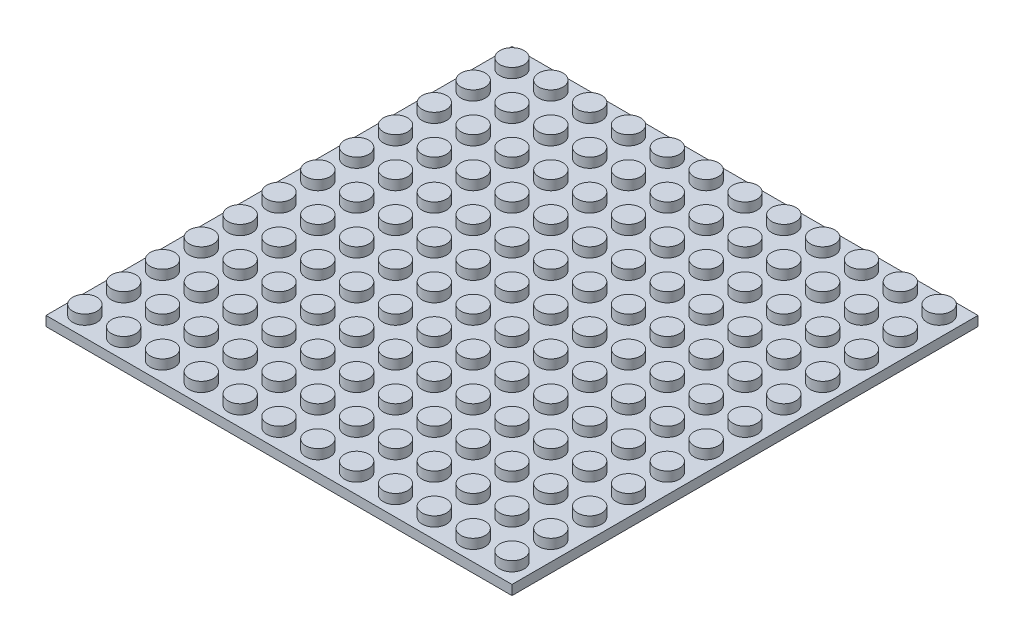
SolidWorks part; units mm, degrees
ref_plane "Front Plane" through (0, 0, 0) normal (0, 0, 1) x (1, 0, 0)
ref_plane "Top Plane" through (0, 0, 0) normal (0, 1, 0) x (1, 0, 0)
ref_plane "Right Plane" through (0, 0, 0) normal (1, 0, 0) x (0, 0, -1)
sketch "Sketch1" plane through (0, 0, 0) normal (0, 1, 0) x (1, 0, 0)
  line L1 (0, 0) -> (96, 0)
  line L2 (0, 0) -> (0, 96)
  line L3 (0, 96) -> (96, 96)
  line L4 (96, 0) -> (96, 96)
  dimension "D1" = 96
  dimension "D2" = 96
extrude "Boss-Extrude1" add sketch "Sketch1" along normal blind 2
sketch "Sketch2" plane through (0, 2, 0) normal (0, 1, 0) x (1, 0, 0)
  line L0 (0, 0) -> (96, 0) construction
  line L1 (0, 96) -> (0, 0) construction
  line L2 (4, 4) -> (12, 4) construction
  circle A0 centre (4, 4) radius 2.5
  circle A1 centre (12, 4) radius 2.5
  circle A2 centre (20, 4) radius 2.5
  circle A3 centre (28, 4) radius 2.5
  circle A4 centre (36, 4) radius 2.5
  circle A5 centre (44, 4) radius 2.5
  circle A6 centre (52, 4) radius 2.5
  circle A7 centre (60, 4) radius 2.5
  circle A8 centre (68, 4) radius 2.5
  circle A9 centre (76, 4) radius 2.5
  circle A10 centre (84, 4) radius 2.5
  circle A11 centre (92, 4) radius 2.5
  circle A12 centre (12, 12) radius 2.5
  circle A13 centre (20, 12) radius 2.5
  circle A14 centre (28, 12) radius 2.5
  circle A15 centre (36, 12) radius 2.5
  circle A16 centre (44, 12) radius 2.5
  circle A17 centre (52, 12) radius 2.5
  circle A18 centre (60, 12) radius 2.5
  circle A19 centre (68, 12) radius 2.5
  circle A20 centre (76, 12) radius 2.5
  circle A21 centre (84, 12) radius 2.5
  circle A22 centre (92, 12) radius 2.5
  circle A23 centre (12, 20) radius 2.5
  circle A24 centre (20, 20) radius 2.5
  circle A25 centre (28, 20) radius 2.5
  circle A26 centre (36, 20) radius 2.5
  circle A27 centre (44, 20) radius 2.5
  circle A28 centre (52, 20) radius 2.5
  circle A29 centre (60, 20) radius 2.5
  circle A30 centre (68, 20) radius 2.5
  circle A31 centre (76, 20) radius 2.5
  circle A32 centre (84, 20) radius 2.5
  circle A33 centre (92, 20) radius 2.5
  circle A34 centre (12, 28) radius 2.5
  circle A35 centre (20, 28) radius 2.5
  circle A36 centre (28, 28) radius 2.5
  circle A37 centre (36, 28) radius 2.5
  circle A38 centre (44, 28) radius 2.5
  circle A39 centre (52, 28) radius 2.5
  circle A40 centre (60, 28) radius 2.5
  circle A41 centre (68, 28) radius 2.5
  circle A42 centre (76, 28) radius 2.5
  circle A43 centre (84, 28) radius 2.5
  circle A44 centre (92, 28) radius 2.5
  circle A45 centre (12, 36) radius 2.5
  circle A46 centre (20, 36) radius 2.5
  circle A47 centre (28, 36) radius 2.5
  circle A48 centre (36, 36) radius 2.5
  circle A49 centre (44, 36) radius 2.5
  circle A50 centre (52, 36) radius 2.5
  circle A51 centre (60, 36) radius 2.5
  circle A52 centre (68, 36) radius 2.5
  circle A53 centre (76, 36) radius 2.5
  circle A54 centre (84, 36) radius 2.5
  circle A55 centre (92, 36) radius 2.5
  circle A56 centre (12, 44) radius 2.5
  circle A57 centre (20, 44) radius 2.5
  circle A58 centre (28, 44) radius 2.5
  circle A59 centre (36, 44) radius 2.5
  circle A60 centre (44, 44) radius 2.5
  circle A61 centre (52, 44) radius 2.5
  circle A62 centre (60, 44) radius 2.5
  circle A63 centre (68, 44) radius 2.5
  circle A64 centre (76, 44) radius 2.5
  circle A65 centre (84, 44) radius 2.5
  circle A66 centre (92, 44) radius 2.5
  circle A67 centre (12, 52) radius 2.5
  circle A68 centre (20, 52) radius 2.5
  circle A69 centre (28, 52) radius 2.5
  circle A70 centre (36, 52) radius 2.5
  circle A71 centre (44, 52) radius 2.5
  circle A72 centre (52, 52) radius 2.5
  circle A73 centre (60, 52) radius 2.5
  circle A74 centre (68, 52) radius 2.5
  circle A75 centre (76, 52) radius 2.5
  circle A76 centre (84, 52) radius 2.5
  circle A77 centre (92, 52) radius 2.5
  circle A78 centre (12, 60) radius 2.5
  circle A79 centre (20, 60) radius 2.5
  circle A80 centre (28, 60) radius 2.5
  circle A81 centre (36, 60) radius 2.5
  circle A82 centre (44, 60) radius 2.5
  circle A83 centre (52, 60) radius 2.5
  circle A84 centre (60, 60) radius 2.5
  circle A85 centre (68, 60) radius 2.5
  circle A86 centre (76, 60) radius 2.5
  circle A87 centre (84, 60) radius 2.5
  circle A88 centre (92, 60) radius 2.5
  circle A89 centre (12, 68) radius 2.5
  circle A90 centre (20, 68) radius 2.5
  circle A91 centre (28, 68) radius 2.5
  circle A92 centre (36, 68) radius 2.5
  circle A93 centre (44, 68) radius 2.5
  circle A94 centre (52, 68) radius 2.5
  circle A95 centre (60, 68) radius 2.5
  circle A96 centre (68, 68) radius 2.5
  circle A97 centre (76, 68) radius 2.5
  circle A98 centre (84, 68) radius 2.5
  circle A99 centre (92, 68) radius 2.5
  circle A100 centre (12, 76) radius 2.5
  circle A101 centre (20, 76) radius 2.5
  circle A102 centre (28, 76) radius 2.5
  circle A103 centre (36, 76) radius 2.5
  circle A104 centre (44, 76) radius 2.5
  circle A105 centre (52, 76) radius 2.5
  circle A106 centre (60, 76) radius 2.5
  circle A107 centre (68, 76) radius 2.5
  circle A108 centre (76, 76) radius 2.5
  circle A109 centre (84, 76) radius 2.5
  circle A110 centre (92, 76) radius 2.5
  circle A111 centre (12, 84) radius 2.5
  circle A112 centre (20, 84) radius 2.5
  circle A113 centre (28, 84) radius 2.5
  circle A114 centre (36, 84) radius 2.5
  circle A115 centre (44, 84) radius 2.5
  circle A116 centre (52, 84) radius 2.5
  circle A117 centre (60, 84) radius 2.5
  circle A118 centre (68, 84) radius 2.5
  circle A119 centre (76, 84) radius 2.5
  circle A120 centre (84, 84) radius 2.5
  circle A121 centre (92, 84) radius 2.5
  circle A122 centre (12, 92) radius 2.5
  circle A123 centre (20, 92) radius 2.5
  circle A124 centre (28, 92) radius 2.5
  circle A125 centre (36, 92) radius 2.5
  circle A126 centre (44, 92) radius 2.5
  circle A127 centre (52, 92) radius 2.5
  circle A128 centre (60, 92) radius 2.5
  circle A129 centre (68, 92) radius 2.5
  circle A130 centre (76, 92) radius 2.5
  circle A131 centre (84, 92) radius 2.5
  circle A132 centre (92, 92) radius 2.5
  circle A133 centre (4, 12) radius 2.5
  circle A134 centre (4, 20) radius 2.5
  circle A135 centre (4, 28) radius 2.5
  circle A136 centre (4, 36) radius 2.5
  circle A137 centre (4, 44) radius 2.5
  circle A138 centre (4, 52) radius 2.5
  circle A139 centre (4, 60) radius 2.5
  circle A140 centre (4, 68) radius 2.5
  circle A141 centre (4, 76) radius 2.5
  circle A142 centre (4, 84) radius 2.5
  circle A143 centre (4, 92) radius 2.5
  dimension "D1" = 5
  dimension "D2" = 4
  dimension "D3" = 4
  dimension "D6" = 8
  dimension "D4" = 12
  dimension "D5" = 12
extrude "Boss-Extrude2" add sketch "Sketch2" along normal blind 2
